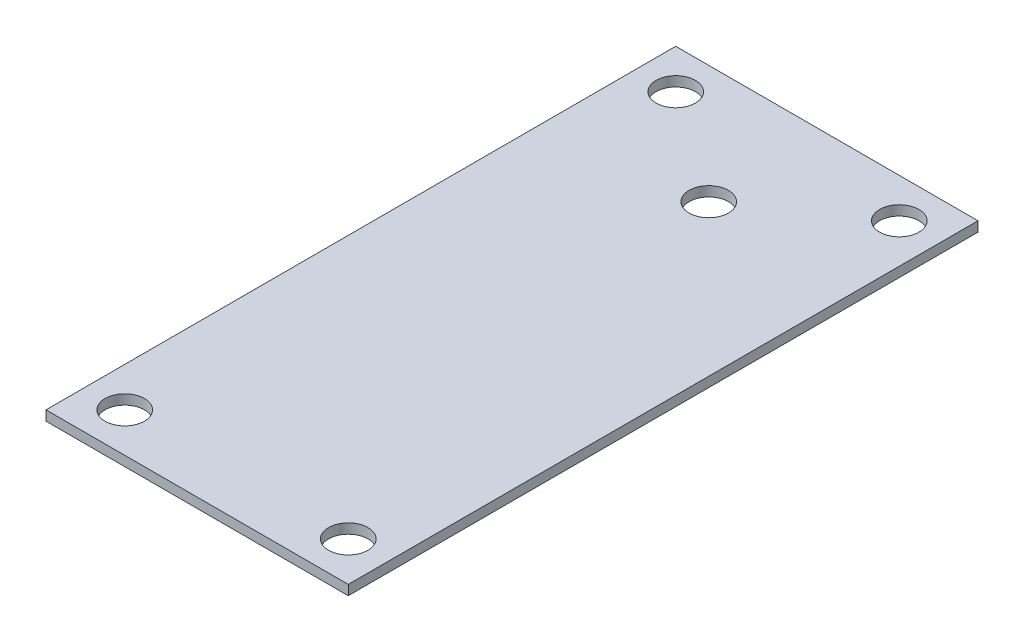
SolidWorks part; units mm, degrees
ref_plane "Front Plane" through (0, 0, 0) normal (0, 0, 1) x (1, 0, 0)
ref_plane "Top Plane" through (0, 0, 0) normal (0, 1, 0) x (1, 0, 0)
ref_plane "Right Plane" through (0, 0, 0) normal (1, 0, 0) x (0, 0, -1)
sketch "Sketch1" plane through (0, 0, 0) normal (0, 1, 0) x (1, 0, 0)
  line L0 (-18.034, 44.45) -> (-18.034, -44.45) construction
  line L1 (-24.384, 50.8) -> (24.384, 50.8)
  line L2 (-24.384, 50.8) -> (-24.384, -50.8)
  line L3 (-24.384, -50.8) -> (24.384, -50.8)
  line L4 (24.384, 50.8) -> (24.384, -50.8)
  line L5 (-14.605, 50.8) -> (14.605, 50.8) construction
  line L6 (-14.605, 50.8) -> (-14.605, -50.8) construction
  line L7 (-14.605, -50.8) -> (14.605, -50.8) construction
  line L8 (14.605, 50.8) -> (14.605, -50.8) construction
  line L9 (-18.034, 44.45) -> (18.034, 44.45) construction
  circle A0 centre (-18.034, 44.45) radius 3.175
  circle A1 centre (18.034, 44.45) radius 3.175
  circle A2 centre (18.034, -44.45) radius 3.175
  circle A3 centre (-18.034, -44.45) radius 3.175
  circle A4 centre (-18.034, -6.35) radius 3.175
  circle A5 centre (18.034, -6.35) radius 3.175
  point P8 (0, 50.8)
  point P9 (0, -50.8)
  point P10 (24.384, 0)
  point P20 (-18.034, 0)
  point P21 (0, 44.45)
  point P26 (0, 0)
  point P27 (0, 0)
  point P28 (-22.225, -17.1187)
  point P31 (19.05, 44.45)
  dimension "D4" = 6.35
  dimension "D2" = 29.718
  dimension "D1" = 101.6
  dimension "D3" = 29.21
  dimension "D5" = 6.35
  dimension "D6" = 6.35
  dimension "D7" = 38.1
extrude "Boss-Extrude1" add sketch "Sketch1" along normal blind 1.5875 contours L4 L1 L2 L3 A5 A4 A3 A2 A1 A0
sketch "Sketch2" plane through (0, 1.5875, 0) normal (0, 1, 0) x (1, 0, 0)
  line L0 (-24.384, 50.8) -> (24.384, 50.8) construction
  circle A0 centre (0, 31.75) radius 3.175
  point P4 (0, 0)
  dimension "D1" = 6.35
  dimension "D2" = 19.05
extrude "Cut-Extrude1" cut sketch "Sketch2" against normal up to next
